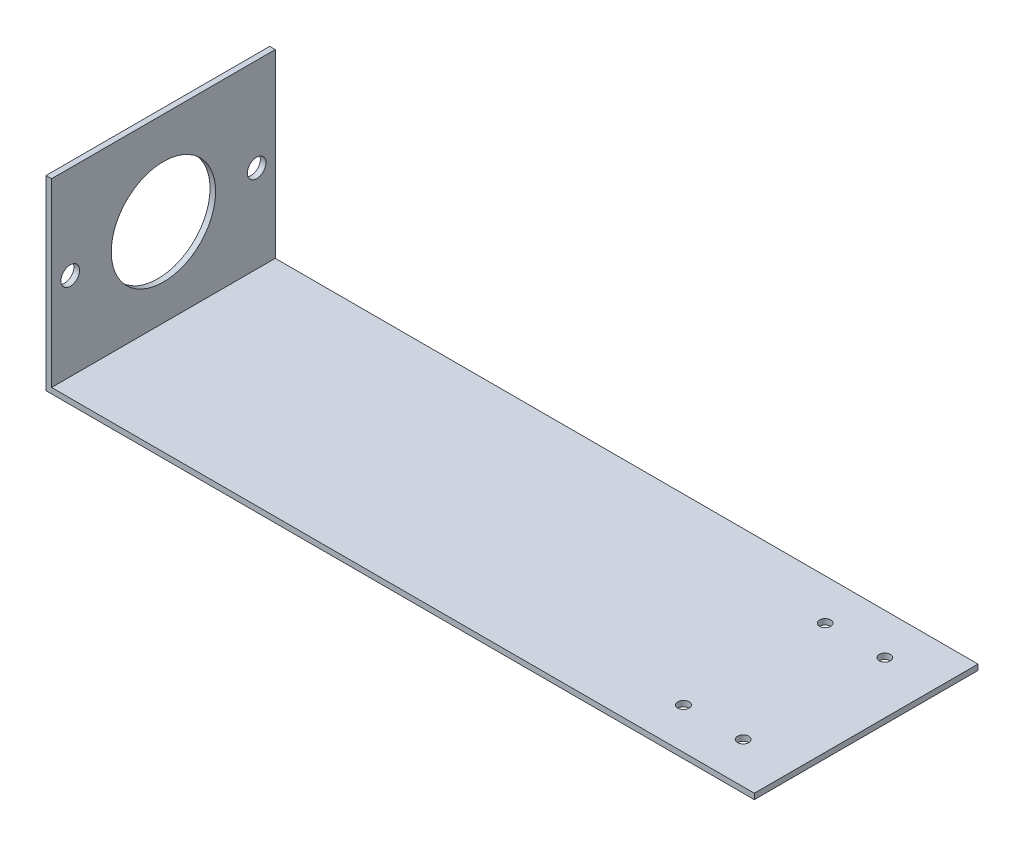
SolidWorks part; units mm, degrees
ref_plane "Front Plane" through (0, 0, 0) normal (0, 0, 1) x (1, 0, 0)
ref_plane "Top Plane" through (0, 0, 0) normal (0, 1, 0) x (1, 0, 0)
ref_plane "Right Plane" through (0, 0, 0) normal (1, 0, 0) x (0, 0, -1)
sketch "Sketch1" plane through (0, 0, 0) normal (0, 0, 1) x (1, 0, 0)
  line L0 (0, 0) -> (0, 50)
  line L1 (0, 50) -> (1.5, 50)
  line L2 (1.5, 50) -> (1.5, 1.5)
  line L3 (1.5, 1.5) -> (190, 1.5)
  line L4 (190, 1.5) -> (190, 0)
  line L5 (190, 0) -> (0, 0)
  dimension "D1" = 50
  dimension "D2" = 1.5
  dimension "D3" = 1.5
  dimension "D4" = 190
extrude "Boss-Extrude1" add sketch "Sketch1" along normal blind 60
sketch "Sketch2" plane through (1.5, 0, 0) normal (1, 0, 0) x (0, 0, -1)
  line L0 (-30, 50) -> (-30, 1.5) construction
  line L1 (-60, 50) -> (0, 50) construction
  line L2 (-60, 1.5) -> (0, 1.5) construction
  circle A0 centre (-30, 25) radius 14
  circle A1 centre (-55, 25) radius 2.5
  circle A2 centre (-5, 25) radius 2.5
  point P12 (0, 0)
  dimension "D1" = 28
  dimension "D2" = 25
  dimension "D3" = 5
  dimension "D4" = 25
extrude "Cut-Extrude1" cut sketch "Sketch2" against normal up to next
sketch "Sketch3" plane through (0, 1.5, 0) normal (0, 1, 0) x (1, 0, 0)
  line L0 (190, -30) -> (1.5, -30) construction
  line L1 (190, -60) -> (190, 0) construction
  line L2 (1.5, -60) -> (1.5, 0) construction
  circle A0 centre (160, -11) radius 1.5
  circle A1 centre (176, -11) radius 1.5
  circle A2 centre (176, -49) radius 1.5
  circle A3 centre (160, -49) radius 1.5
  point P10 (0, 0)
  point P11 (0, 0)
  dimension "D2" = 16
  dimension "D3" = 38
  dimension "D4" = 3
  dimension "D1" = 14
extrude "Cut-Extrude2" cut sketch "Sketch3" against normal up to next
